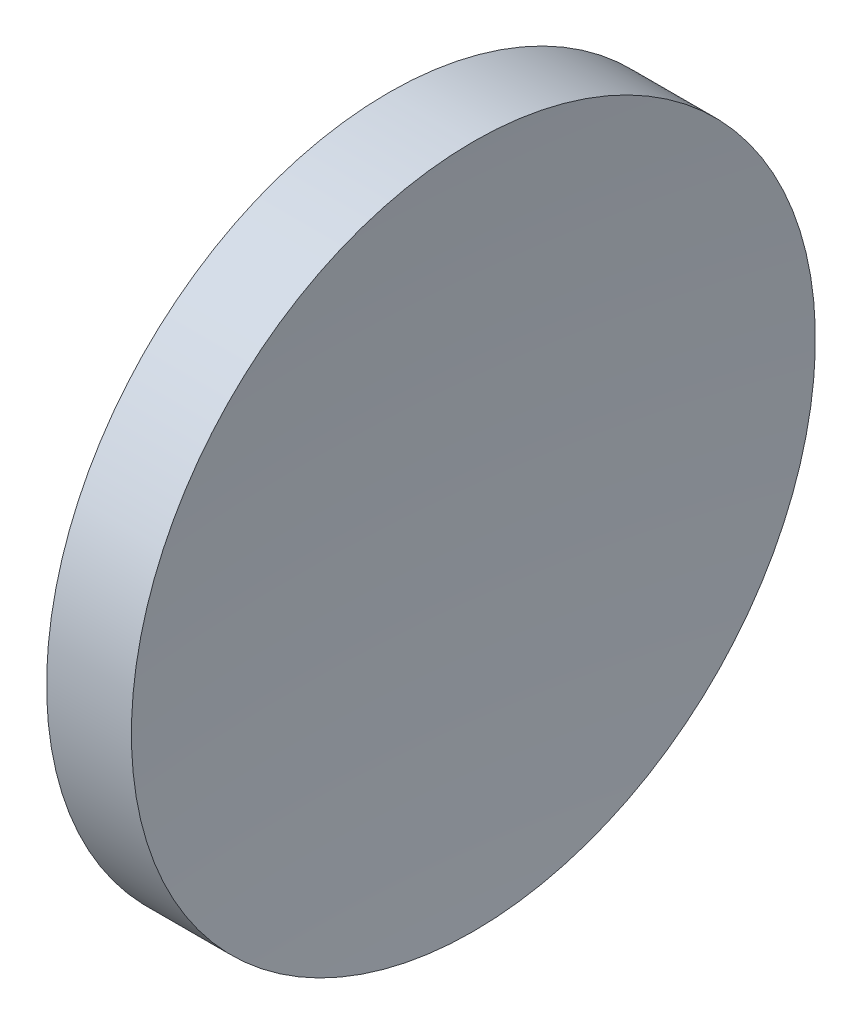
SolidWorks part; units mm, degrees
ref_plane "前视基准面" through (0, 0, 0) normal (0, 0, 1) x (1, 0, 0)
ref_plane "上视基准面" through (0, 0, 0) normal (0, 1, 0) x (1, 0, 0)
ref_plane "右视基准面" through (0, 0, 0) normal (1, 0, 0) x (0, 0, -1)
sketch "草图1" plane through (0, 0, 0) normal (0, 0, 1) x (1, 0, 0)
  line L0 (89.8587, 52.1781) -> (104.0854, 52.1781) construction
  line L1 (97.0904, 52.1781) -> (95.0904, 52.1781)
  line L3 (96.0904, 64.8781) -> (97.6644, 64.8781)
  line L4 (96.0904, 64.8781) -> (94.5165, 64.8781)
  arc A0 (95.0904, 52.1781) -> (94.5165, 64.8781) centre (-45.7096, 52.1781) ccw
  arc A1 (97.6644, 64.8781) -> (97.0904, 52.1781) centre (237.8904, 52.1781) ccw
revolve "旋转1" add sketch "草图1" angle 360 about L0
